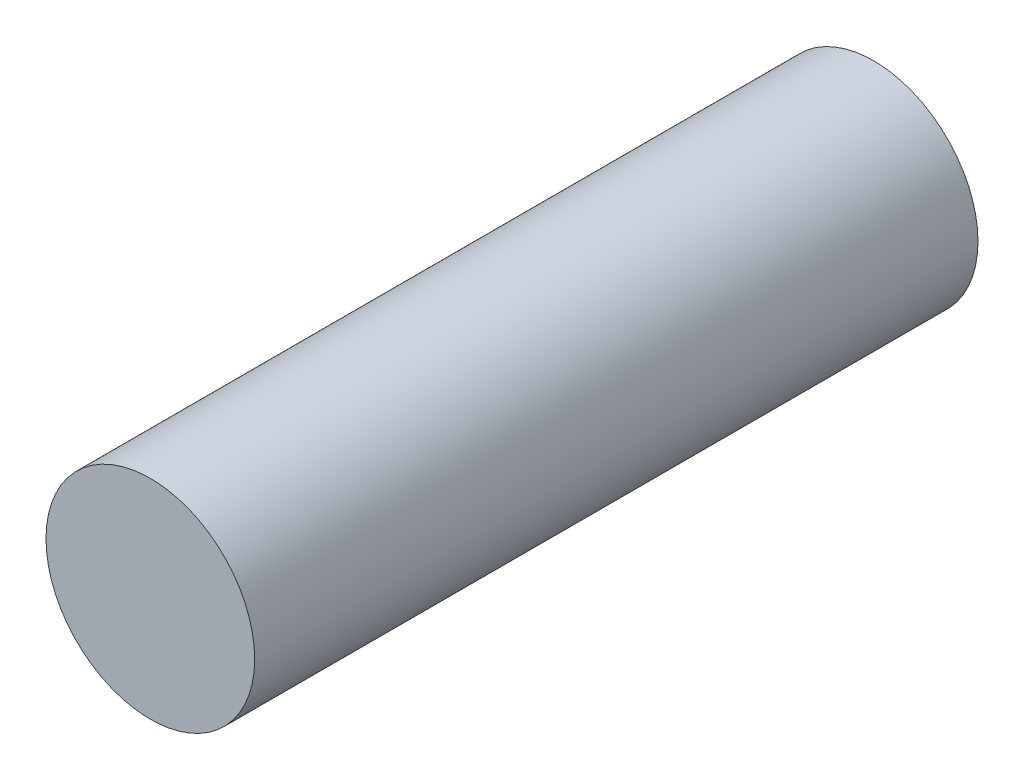
SolidWorks part; units mm, degrees
ref_plane "Спереди" through (0, 0, 0) normal (0, 0, 1) x (1, 0, 0)
ref_plane "Сверху" through (0, 0, 0) normal (0, 1, 0) x (1, 0, 0)
ref_plane "Справа" through (0, 0, 0) normal (1, 0, 0) x (0, 0, -1)
sketch "Эскиз1" plane through (0, 0, 0) normal (0, 0, 1) x (1, 0, 0)
  circle A0 centre (0, 0) radius 7.025
  point P2 (0, 0)
  dimension "D1" = 14.05
extrude "Бобышка-Вытянуть1" add sketch "Эскиз1" along normal blind 48.7
